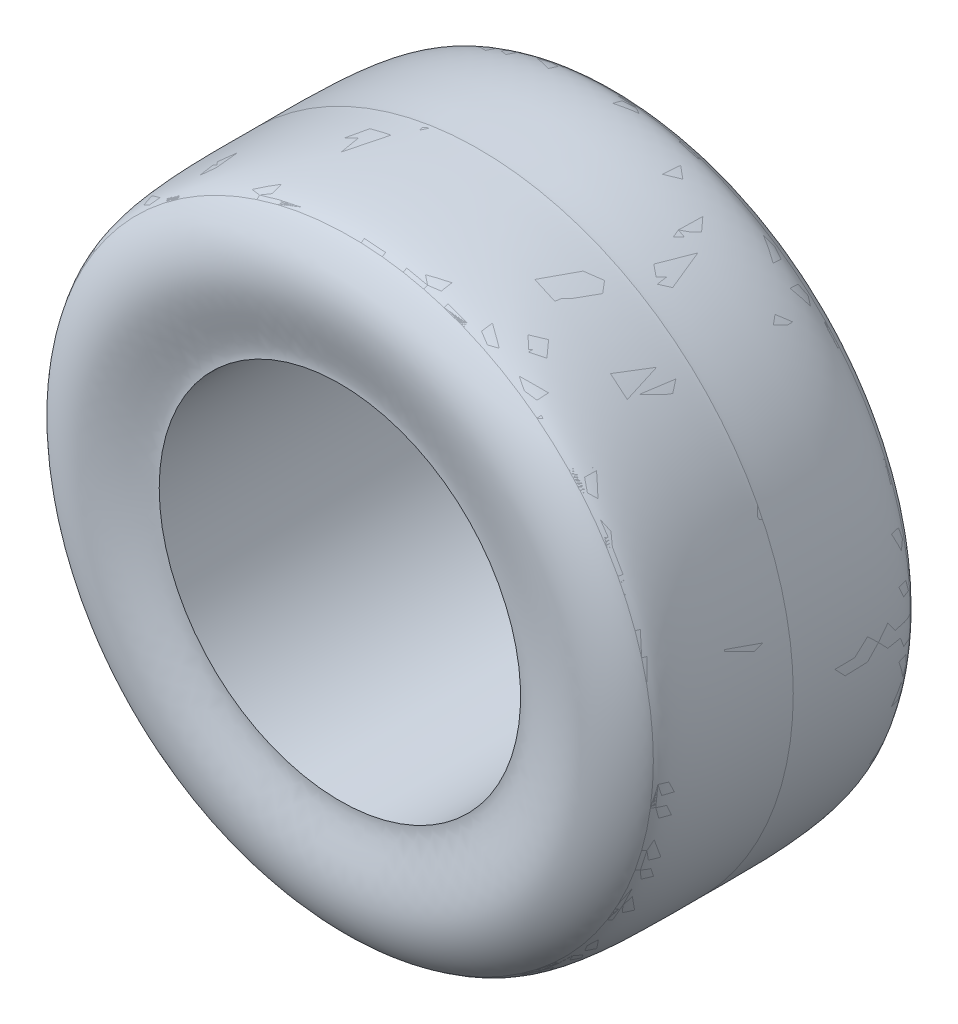
SolidWorks part; units mm, degrees
ref_plane "Front Plane" through (0, 0, 0) normal (0, 0, 1) x (1, 0, 0)
ref_plane "Top Plane" through (0, 0, 0) normal (0, 1, 0) x (1, 0, 0)
ref_plane "Right Plane" through (0, 0, 0) normal (1, 0, 0) x (0, 0, -1)
sketch "Sketch1" plane through (0, 0, 0) normal (1, 0, 0) x (0, 0, -1)
  line L0 (-146.2514, 0) -> (150.7057, 0)
  line L1 (-146.2514, 287) -> (146.2514, 287) construction
  line L2 (0, 332.4015) -> (0, 0) construction
  line L3 (-127, 165) -> (127, 165) construction
  line L4 (194.8975, 0) -> (-184.306, 0)
  line L5 (-152.2698, 276.5073) -> (136.2911, 276.5073) construction
  line L6 (-117.2862, 276.5073) -> (117.2862, 276.5073)
  spline S0 degree 3 poles (0, 287) (-4.0793, 286.8267) (-106.0619, 288.284) (-113.6063, 278.8801) (-117.2862, 276.5073) knots 0 0 0 0 0.064751 0.299258 0.299258 0.299258 0.299258
  spline S1 degree 3 poles (0, 287) (4.0793, 286.8267) (106.0619, 288.284) (113.6063, 278.8801) (117.2862, 276.5073) knots 0 0 0 0 0.064751 0.299258 0.299258 0.299258 0.299258
  spline S2 degree 3 poles (117.2862, 276.5073) (117.5261, 276.3526) (123.1962, 273.0331) (155.2071, 236.2106) (126.0194, 177.982) (127, 165) knots 0.299258 0.299258 0.299258 0.299258 0.314545 0.697278 1 1 1 1 construction
  spline S3 degree 3 poles (-117.2862, 276.5073) (-117.5261, 276.3526) (-123.1962, 273.0331) (-155.2071, 236.2106) (-126.0194, 177.982) (-127, 165) knots 0.299258 0.299258 0.299258 0.299258 0.314545 0.697278 1 1 1 1 construction
  point P20 (117.2862, 276.5073)
  point P21 (-117.2862, 276.5073)
  dimension "D1" = 287
  dimension "D2" = 140
  dimension "D3" = 127
  dimension "D4" = 165
revolve "Revolve1" add sketch "Sketch1"
sketch "Sketch7" plane through (0, 0, 0) normal (1, 0, 0) x (0, 0, -1)
  line L0 (194.8975, 0) -> (-184.306, 0) construction
  line L1 (-117.2862, 276.5073) -> (117.2862, 276.5073)
  line L2 (-117.2862, 276.5073) -> (117.2862, 276.5073)
  line L4 (194.8975, 0) -> (-184.306, 0) construction
  line L6 (-127, 165) -> (127, 165) construction
  line L7 (-127, 165) -> (127, 165)
  spline S0 degree 3 poles (1105.6715, 1858.9531) (-121.3435, 260.1151) (-101.9659, 297.4544) (-204.1636, 179.8957) (113.1388, -58.3859) (-1797.9281, 1263.086) knots -0.165488 -0.165488 -0.165488 -0.165488 0.314545 0.697278 2.071691 2.071691 2.071691 2.071691 only from (-117.2862, 276.5073) to (-127, 165) construction
  spline S1 degree 3 poles (-1105.6715, 1858.9531) (121.3435, 260.1151) (101.9659, 297.4544) (204.1636, 179.8957) (-113.1388, -58.3859) (1797.9281, 1263.086) knots -0.165488 -0.165488 -0.165488 -0.165488 0.314545 0.697278 2.071691 2.071691 2.071691 2.071691 only from (117.2862, 276.5073) to (127, 165) construction
  spline S2 degree 3 poles (3008.1605, 1076.6248) (-658.1464, 129.7303) (666.1784, 332.4083) (-280.2601, 273.9263) (2997.2775, 406.5572) knots -0.879722 -0.879722 -0.879722 -0.879722 0.234506 0.587708 0.587708 0.587708 0.587708 only from (117.2862, 276.5073) to (0, 287)
  spline S3 degree 3 poles (-2997.4666, 406.5649) (280.2688, 273.9257) (-666.1866, 332.4093) (658.1522, 129.7295) (-3008.1922, 1076.633) knots -0.288457 -0.288457 -0.288457 -0.288457 0.064751 1.178983 1.178983 1.178983 1.178983 only from (0, 287) to (-117.2862, 276.5073)
  spline S4 degree 3 poles (117.2862, 276.5073) (113.6063, 278.8801) (106.0619, 288.284) (4.0793, 286.8267) (0, 287) knots 0 0 0 0 0.234506 0.299258 0.299258 0.299258 0.299258 construction
  spline S5 degree 3 poles (0, 287) (-4.0793, 286.8267) (-106.0619, 288.284) (-113.6063, 278.8801) (-117.2862, 276.5073) knots 0 0 0 0 0.064751 0.299258 0.299258 0.299258 0.299258 construction
  spline S6 degree 3 poles (-117.2862, 276.5073) (-117.5261, 276.3526) (-123.1962, 273.0331) (-155.2071, 236.2106) (-126.0194, 177.982) (-127, 165) knots 0.299258 0.299258 0.299258 0.299258 0.314545 0.697278 1 1 1 1
  spline S7 degree 3 poles (117.2862, 276.5073) (117.5261, 276.3526) (123.1962, 273.0331) (155.2071, 236.2106) (126.0194, 177.982) (127, 165) knots 0.299258 0.299258 0.299258 0.299258 0.314545 0.697278 1 1 1 1
  dimension "D1" = 0
revolve "Revolve2" add sketch "Sketch7" angle 360 about L4
sketch "Sketch3" plane through (0, 0, 0) normal (1, 0, 0) x (0, 0, -1)
  line L0 (-127, 0) -> (0, 0) construction
  dimension "D1" = 127
sketch "Sketch4" plane through (0, 0, 0) normal (0, 0, 1) x (1, 0, 0)
  line L0 (0, 0) -> (0, -287) construction
  dimension "D1" = 287
sketch "Sketch5" plane through (0, 0, 0) normal (1, 0, 0) x (0, 0, -1)
  line L0 (0, -287) -> (-140, -287) construction
  line L1 (0, 0) -> (0, -287) construction
  dimension "D1" = 140
surface "Surface-Knit1"
